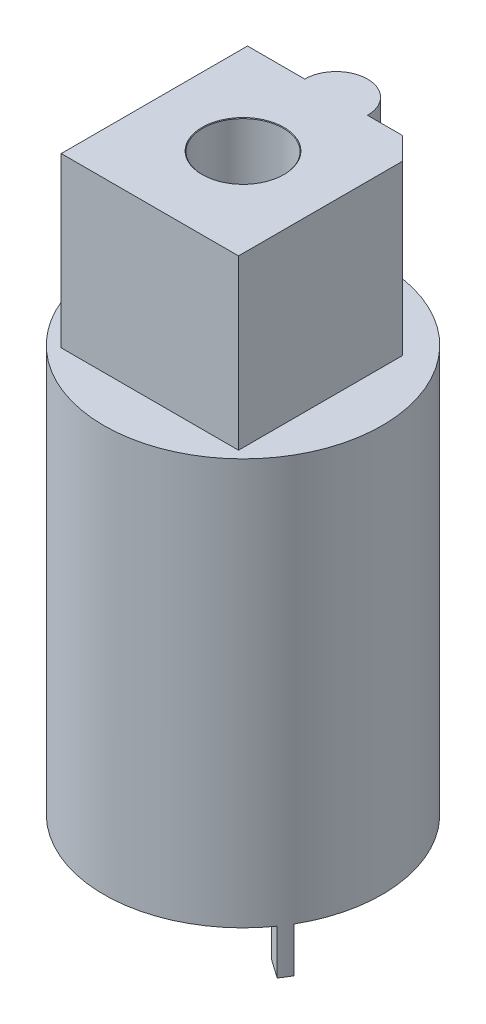
SolidWorks part; units mm, degrees
ref_plane "Plano frontal" through (0, 0, 0) normal (0, 0, 1) x (1, 0, 0)
ref_plane "Plano superior" through (0, 0, 0) normal (0, 1, 0) x (1, 0, 0)
ref_plane "Plano direito" through (0, 0, 0) normal (1, 0, 0) x (0, 0, -1)
sketch "Esboço1" plane through (0, 0, 0) normal (0, 1, 0) x (1, 0, 0)
  circle A0 centre (0, 0) radius 6.2
  dimension "D1" = 12.4
extrude "Ressalto-extrusão1" add sketch "Esboço1" along normal blind 18.1
sketch "Esboço2" plane through (0, 0, 0) normal (0, 1, 0) x (1, 0, 0)
  line L0 (0, 0) -> (0, 6.2) construction
  line L1 (0, 0) -> (5.3694, 3.1) construction
  line L2 (4.5033, -2.6) -> (5.3694, -3.1)
  line L3 (0, 0) -> (0, -6.2) construction
  line L4 (0, 0) -> (-5.3694, -3.1) construction
  line L5 (0, 0) -> (-5.3694, 3.1) construction
  line L6 (4.2596, -2.9826) -> (5.0787, -3.5562)
  line L7 (0, 0) -> (4.2596, -2.9826) construction
  line L8 (0, 0) -> (4.5033, -2.6) construction
  circle A0 centre (0, 0) radius 6.2 construction
  arc A1 (5.0787, -3.5562) -> (5.3694, -3.1) centre (0, 0) ccw
  arc A2 (4.2596, -2.9826) -> (4.5033, -2.6) centre (0, 0) ccw
  arc A3 (4.5033, -2.6) -> (4.5033, 2.6) centre (0, 0) ccw construction
  arc A4 (5.3694, -3.1) -> (5.3694, 3.1) centre (0, 0) ccw construction
  arc A5 (5.3694, 3.1) -> (0, 6.2) centre (0, 0) ccw construction
  arc A6 (4.5033, 2.6) -> (0, 5.2) centre (0, 0) ccw construction
  arc A7 (0, 5.2) -> (-4.5033, 2.6) centre (0, 0) ccw construction
  arc A8 (0, 6.2) -> (-5.3694, 3.1) centre (0, 0) ccw construction
  arc A9 (-5.3694, 3.1) -> (-5.3694, -3.1) centre (0, 0) ccw construction
  arc A10 (-4.5033, 2.6) -> (-4.5033, -2.6) centre (0, 0) ccw construction
  arc A11 (-4.5033, -2.6) -> (0, -5.2) centre (0, 0) ccw construction
  arc A12 (-5.3694, -3.1) -> (0, -6.2) centre (0, 0) ccw construction
  arc A13 (0, -6.2) -> (5.0787, -3.5562) centre (0, 0) ccw construction
  arc A14 (0, -5.2) -> (4.2596, -2.9826) centre (0, 0) ccw construction
  point P12 (0, 0)
  point P13 (0, -5.2)
  dimension "D2" = 1
  dimension "D3" = 5
  dimension "D1" = 6
extrude "Ressalto-extrusão2" add sketch "Esboço2" against normal blind 2
sketch "Esboço3" plane through (0, 18.1, 0) normal (0, 1, 0) x (1, 0, 0)
  line L0 (1.4, 4.15) -> (3.95, 4.15)
  line L1 (-3.95, 4.15) -> (-1.4, 4.15)
  line L2 (-3.95, 4.15) -> (-3.95, -4.15)
  line L3 (-3.95, -4.15) -> (3.95, -4.15)
  line L4 (3.95, 4.15) -> (3.95, -4.15)
  line L5 (-3.95, 4.15) -> (3.95, -4.15) construction
  line L6 (-3.95, -4.15) -> (3.95, 4.15) construction
  line L7 (-1.4, 4.15) -> (1.4, 4.15) construction
  arc A0 (1.4, 4.15) -> (-1.4, 4.15) centre (0, 4.15) ccw
  arc A1 (-1.4, 4.15) -> (1.4, 4.15) centre (0, 4.15) ccw construction
  point P0 (0, 0)
  point P7 (0, 0)
  dimension "D3" = 2.8
  dimension "D1" = 7.9
  dimension "D2" = 8.3
extrude "Ressalto-extrusão3" add sketch "Esboço3" along normal blind 7.5
chamfer "Chanfro1" distance 1 angle 45 1 edges at (3.95, 21.85, -4.15)
sketch "Esboço4" plane through (0, 25.6, 0) normal (0, 1, 0) x (1, 0, 0)
  point P0 (0, 0)
hole_wizard "Furo de diâmetro Ø3.6 (3.6)1" positions "Esboço4" profile "Esboço6" hole size "Ø3.6" standard "Ansi Metric"
sketch "Esboço6" plane through (0, 25.6, 0) normal (1, 0, 0) x (0, 0, 1)
  line L0 (0, 0) -> (0, 11.0815)
  line L1 (0, 11.0815) -> (1.8, 10)
  line L2 (1.8, 10) -> (1.8, 0.025)
  line L3 (1.8, 0.025) -> (1.825, 0)
  line L5 (1.825, 0) -> (0, 0)
  line L6 (-1.8, 0.025) -> (-1.825, 0) construction
  line L10 (0, 11.0815) -> (-1.8, 10) construction
  line L11 (0, -6.35) -> (0, 107.95) construction
  dimension "Hole Dia." = 3.6
  dimension "Hole Depth" = 10
  dimension "Near C'Sink Dia." = 3.65
  dimension "Near C'Sink Angle" = 90
  dimension "Drill Angle" = 118
